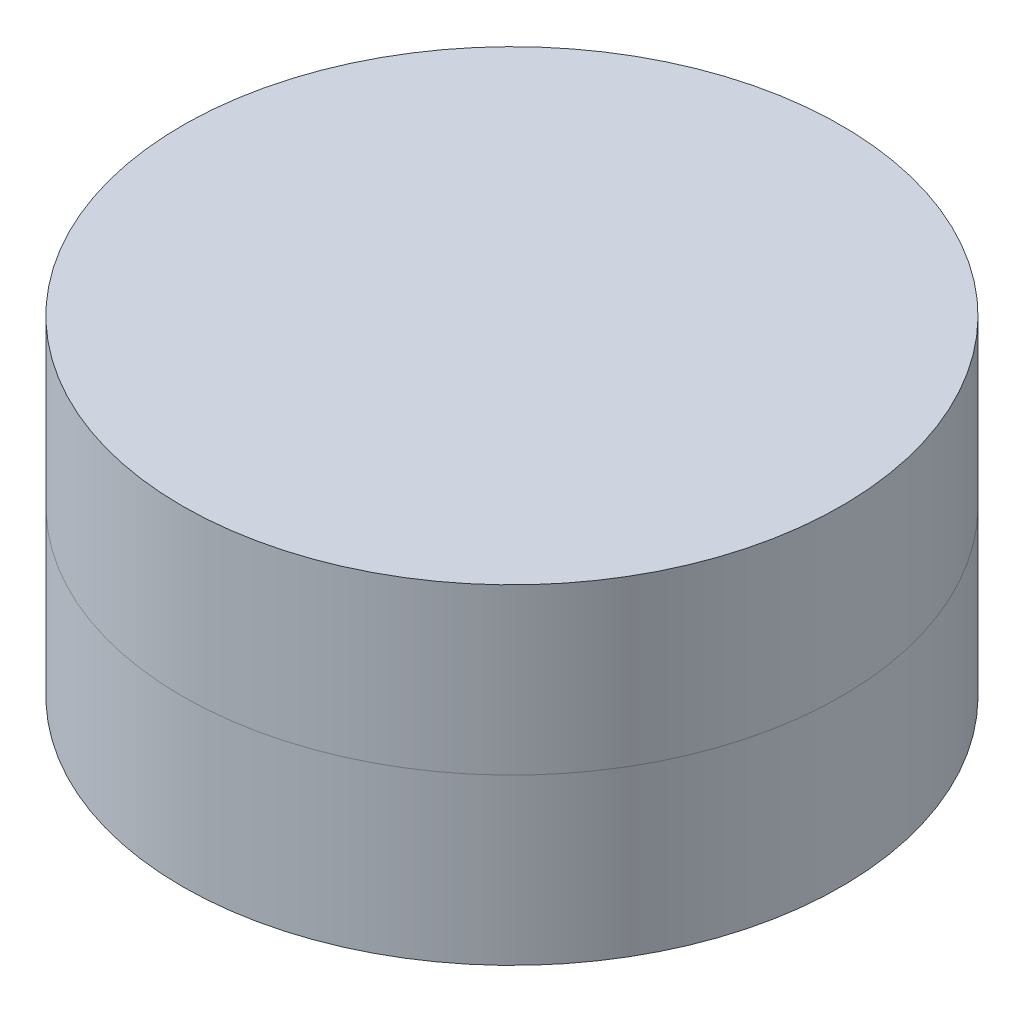
SolidWorks part; units mm, degrees
ref_plane "Front Plane" through (0, 0, 0) normal (0, 0, 1) x (1, 0, 0)
ref_plane "Top Plane" through (0, 0, 0) normal (0, 1, 0) x (1, 0, 0)
ref_plane "Right Plane" through (0, 0, 0) normal (1, 0, 0) x (0, 0, -1)
sketch "Sketch1" plane through (0, 0, 0) normal (0, 1, 0) x (1, 0, 0)
  circle A0 centre (0, 0) radius 4.7625
  dimension "D1" = 9.525
extrude "Boss-Extrude1" add sketch "Sketch1" along normal mid plane 4.7625
split line "Split Line1"
